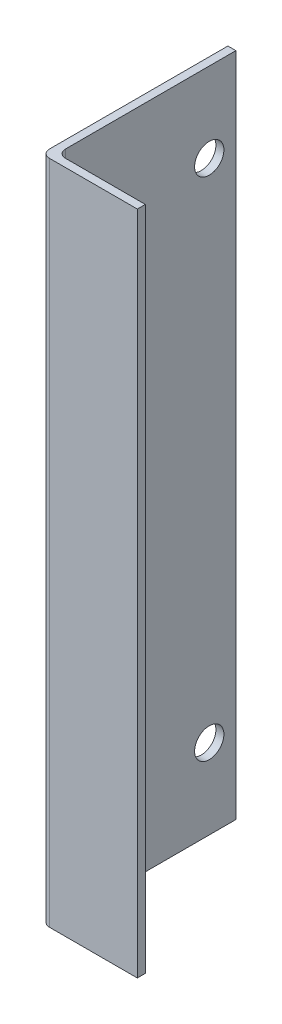
SolidWorks part; units mm, degrees
material "1.0035 (S185)"
ref_plane "Front Plane" through (0, 0, 0) normal (0, 0, 1) x (1, 0, 0)
ref_plane "Top Plane" through (0, 0, 0) normal (0, 1, 0) x (1, 0, 0)
ref_plane "Right Plane" through (0, 0, 0) normal (1, 0, 0) x (0, 0, -1)
sketch "Sketch1" plane through (0, 0, 0) normal (0, 1, 0) x (1, 0, 0)
  line L0 (0, 0) -> (0, 35)
  line L1 (0, 0) -> (18, 0)
  line L2 (0, 35) -> (1.5, 35)
  line L3 (1.5, 35) -> (1.5, 1.5)
  line L4 (1.5, 1.5) -> (18, 1.5)
  line L5 (18, 1.5) -> (18, 0)
  dimension "D1" = 35
  dimension "D2" = 18
  dimension "D3" = 1.5
  dimension "D4" = 1.5
extrude "Boss-Extrude1" add sketch "Sketch1" along normal blind 125
fillet "Fillet1" radius 1.5 1 edges at (1.5, 62.5, -1.5)
fillet "Fillet2" radius 1.5 1 edges at (0, 62.5, 0)
sketch "Sketch2" plane through (1.5, 0, 0) normal (1, 0, 0) x (0, 0, -1)
  circle A0 centre (30, 110) radius 2.75
  circle A1 centre (30, 15) radius 2.75
  point P10 (20.1459, 89.0715)
extrude "Cut-Extrude1" cut sketch "Sketch2" against normal through all
